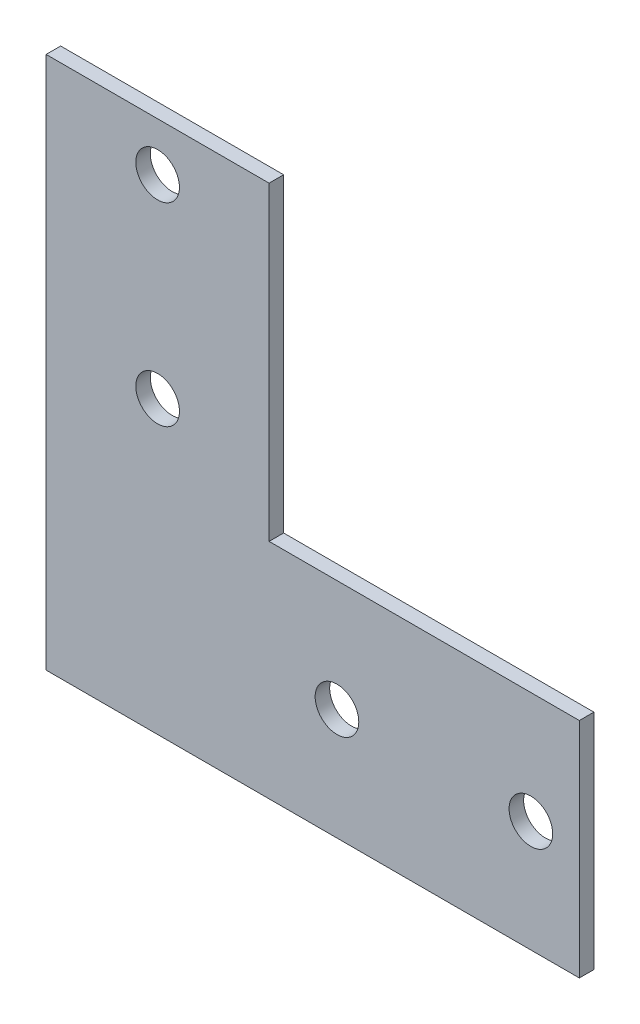
SolidWorks part; units mm, degrees
ref_plane "Спереди" through (0, 0, 0) normal (0, 0, 1) x (1, 0, 0)
ref_plane "Сверху" through (0, 0, 0) normal (0, 1, 0) x (1, 0, 0)
ref_plane "Справа" through (0, 0, 0) normal (1, 0, 0) x (0, 0, -1)
sketch "Эскиз1" plane through (0, 0, 0) normal (0, 0, 1) x (1, 0, 0)
  line L5 (0, 110) -> (0, 0)
  line L6 (0, 0) -> (110, 0)
  line L11 (110, 0) -> (110, 46)
  line L12 (110, 46) -> (46, 46)
  line L16 (46, 46) -> (46, 110)
  line L17 (46, 110) -> (0, 110)
  line L18 (110, 23) -> (100, 23) construction
  line L19 (100, 23) -> (60, 23) construction
  line L20 (23, 110) -> (23, 100) construction
  line L21 (23, 100) -> (23, 60) construction
  circle A6 centre (23, 100) radius 4.5
  circle A7 centre (23, 60) radius 4.5
  circle A8 centre (60, 23) radius 4.5
  circle A9 centre (100, 23) radius 4.5
  dimension "D4" = 10
  dimension "D5" = 40
  dimension "D3" = 9
  dimension "D1" = 110
  dimension "D2" = 46
extrude "Бобышка-Вытянуть1" add sketch "Эскиз1" along normal blind 3
